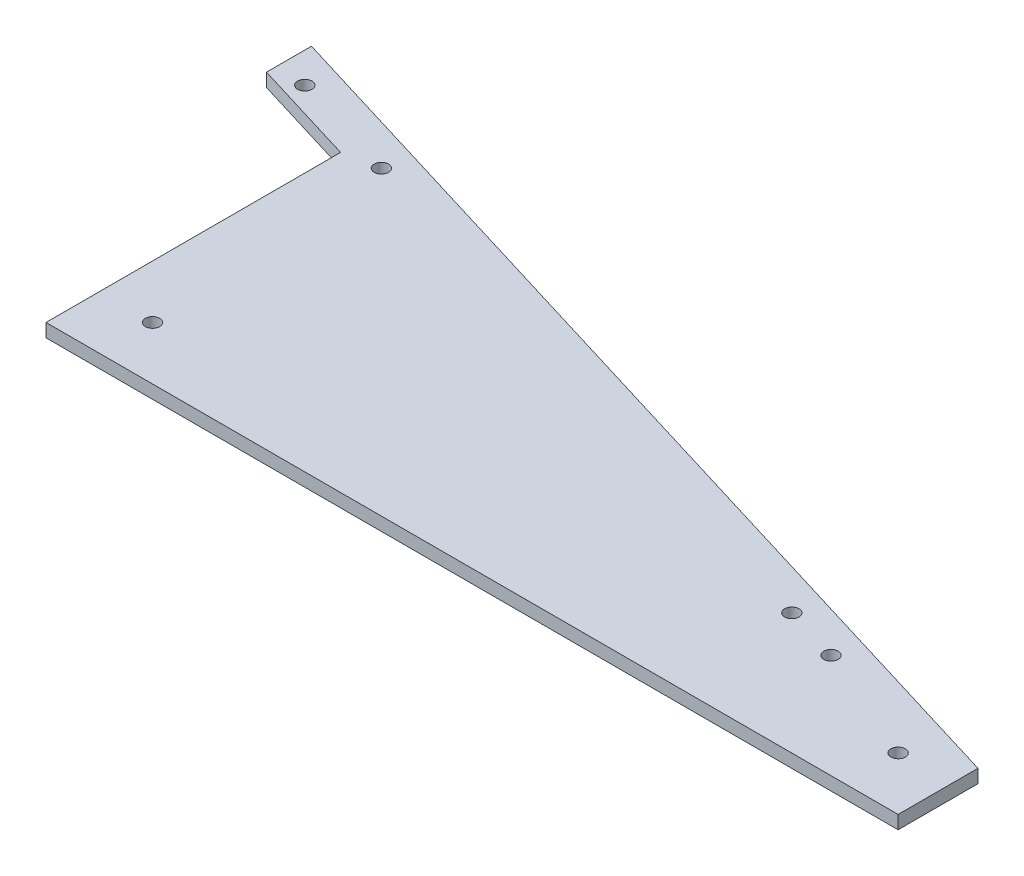
SolidWorks part; units mm, degrees
material "PC High Viscosity"
ref_plane "Front Plane" through (0, 0, 0) normal (0, 0, 1) x (1, 0, 0)
ref_plane "Top Plane" through (0, 0, 0) normal (0, 1, 0) x (1, 0, 0)
ref_plane "Right Plane" through (0, 0, 0) normal (1, 0, 0) x (0, 0, -1)
sketch "Sketch1" plane through (0, 0, 0) normal (0, 1, 0) x (1, 0, 0)
  line L0 (0, 0) -> (406.4, 0)
  line L1 (406.4, 0) -> (406.4, 38.1)
  line L2 (406.4, 38.1) -> (0, 161.925)
  line L3 (0, 161.925) -> (0, 0)
  circle A1 centre (381, 25.4) radius 3.429
  circle A2 centre (25.4, 25.4) radius 3.429
  dimension "D6" = 6.858
  dimension "D1" = 161.925
  dimension "D2" = 406.4
  dimension "D3" = 38.1
  dimension "D4" = 25.4
  dimension "D5" = 25.4
  dimension "D7" = 25.4
extrude "Boss-Extrude1" add sketch "Sketch1" along normal blind 6.35
sketch "Sketch2" plane through (0, 6.35, 0) normal (0, 1, 0) x (1, 0, 0)
  line L7 (0, 161.925) -> (-50.8, 177.4031)
  line L8 (-50.8, 177.4031) -> (-50.8, 155.9612)
  line L9 (-50.8, 155.9612) -> (0, 140.4831)
  line L10 (0, 161.925) -> (0, 0) construction
  line L11 (406.4, 38.1) -> (0, 161.925) construction
  line L12 (0, 140.4831) -> (0, 161.925)
  dimension "D1" = 20.511
  dimension "D2" = 50.8
extrude "Boss-Extrude2" add sketch "Sketch2" against normal blind 6.35
sketch "Sketch3" plane through (0, 6.35, 0) normal (0, 1, 0) x (1, 0, 0)
  line L0 (406.4, 38.1) -> (-50.8, 177.4031) construction
  line L1 (-50.8, 177.4031) -> (-50.8, 155.9612) construction
  line L2 (-50.8, 177.4031) -> (-58.2031, 153.1059) construction
  circle A0 centre (324.6726, 49.7249) radius 3.429
  circle A8 centre (16.2616, 143.6939) radius 3.429
  circle A9 centre (297.811, 57.9093) radius 3.429
  circle A10 centre (-36.2786, 159.7022) radius 3.429
  circle A11 centre (170.4671, 96.7094) radius 3.429 [skipped]
  circle A12 centre (93.3643, 120.2016) radius 3.429 [skipped]
  circle A13 centre (247.5699, 73.2171) radius 3.429 [skipped]
  dimension "D4" = 6.858
  dimension "D6" = 6.858
  dimension "D9" = 6.858
  dimension "D1" = 12.7
  dimension "D2" = 82.55
  dimension "D3" = 5
  dimension "D5" = 67.0616
  dimension "D7" = 12.7
  dimension "D8" = 28.0808
  dimension "D10" = 19.05
  dimension "D11" = 12.7
extrude "Cut-Extrude1" cut sketch "Sketch3" against normal up to next
